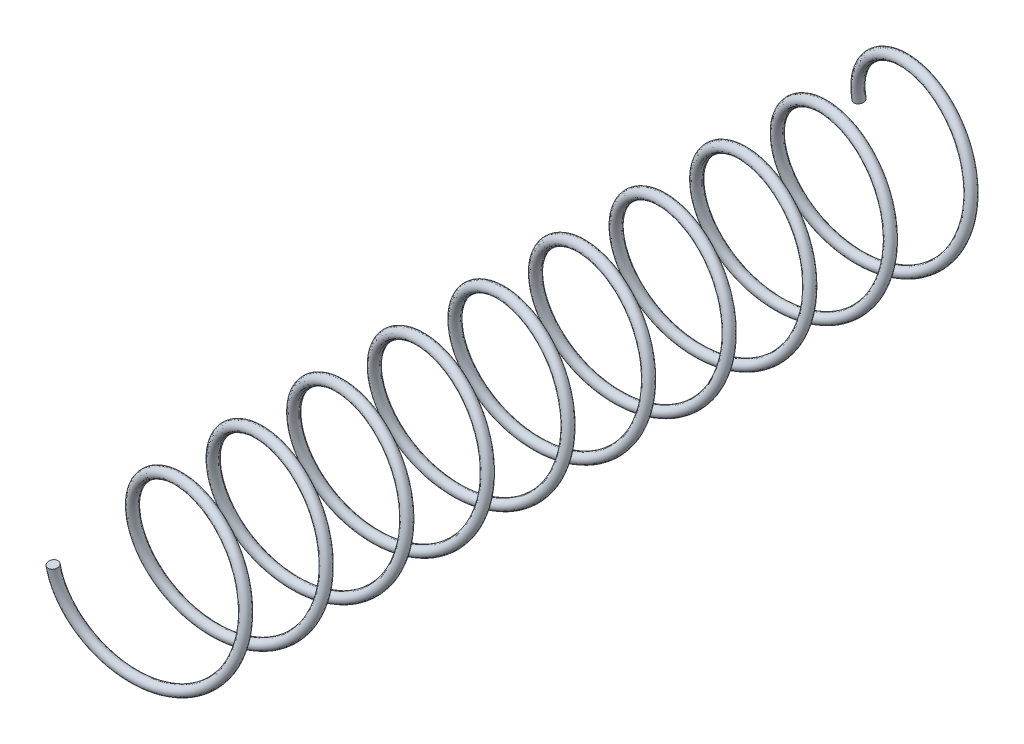
SolidWorks part; units mm, degrees
ref_plane "Front Plane" through (0, 0, 0) normal (0, 0, 1) x (1, 0, 0)
ref_plane "Top Plane" through (0, 0, 0) normal (0, 1, 0) x (1, 0, 0)
ref_plane "Right Plane" through (0, 0, 0) normal (1, 0, 0) x (0, 0, -1)
sketch "Sketch2" plane through (0, 0, 0) normal (0, 0, 1) x (1, 0, 0)
  circle A0 centre (0, 0) radius 7.5
  dimension "D1" = 15
curve "Helix/Spiral2" pitch 8 height 80 turns 10
sweep "Sweep1" add path "Helix/Spiral2" circular profile diameter 1 parameters "D3"=1
